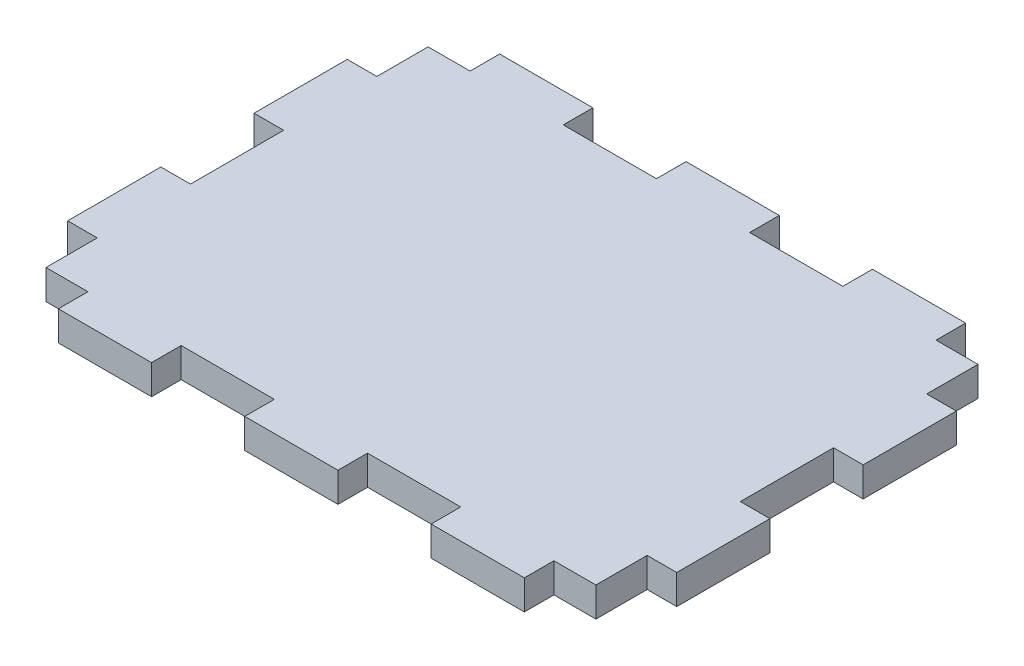
SolidWorks part; units mm, degrees
ref_plane "Front Plane" through (0, 0, 0) normal (0, 0, 1) x (1, 0, 0)
ref_plane "Top Plane" through (0, 0, 0) normal (0, 1, 0) x (1, 0, 0)
ref_plane "Right Plane" through (0, 0, 0) normal (1, 0, 0) x (0, 0, -1)
sketch "Sketch1" plane through (0, 0, 0) normal (0, 1, 0) x (1, 0, 0)
  line L1 (0, 0) -> (65.35, 0)
  line L2 (0, 0) -> (0, 47.35)
  line L3 (0, 47.35) -> (65.35, 47.35)
  line L4 (65.35, 0) -> (65.35, 47.35)
  dimension "D1" = 65.35
  dimension "D2" = 47.35
extrude "Boss-Extrude1" add sketch "Sketch1" along normal blind 3.175
sketch "Sketch2" plane through (0, 0, 0) normal (0, -1, 0) x (1, 0, 0)
  line L0 (65.35, 0) -> (65.35, -47.35) construction
  line L1 (62.175, -38.675) -> (65.35, -38.675)
  line L2 (62.175, -38.675) -> (62.175, -47.35)
  line L3 (62.175, -47.35) -> (65.35, -47.35)
  line L4 (65.35, -38.675) -> (65.35, -47.35)
  line L5 (0, 0) -> (65.35, 0) construction
  line L6 (62.175, -28.675) -> (65.35, -28.675)
  line L7 (62.175, -28.675) -> (62.175, -18.675)
  line L8 (62.175, -18.675) -> (65.35, -18.675)
  line L9 (65.35, -28.675) -> (65.35, -18.675)
  line L10 (62.175, -8.675) -> (65.35, -8.675)
  line L11 (62.175, -8.675) -> (62.175, 0)
  line L12 (62.175, 0) -> (65.35, 0)
  line L13 (65.35, -8.675) -> (65.35, 0)
  line L14 (65.35, -47.35) -> (0, -47.35) construction
  line L15 (0, -47.35) -> (0, 0) construction
  line L16 (0, -47.35) -> (3.175, -47.35)
  line L17 (0, -47.35) -> (0, -38.675)
  line L18 (0, -38.675) -> (3.175, -38.675)
  line L19 (3.175, -47.35) -> (3.175, -38.675)
  line L21 (0, -28.675) -> (3.175, -28.675)
  line L22 (0, -28.675) -> (0, -18.675)
  line L23 (0, -18.675) -> (3.175, -18.675)
  line L24 (3.175, -28.675) -> (3.175, -18.675)
  line L25 (0, 0) -> (3.175, 0)
  line L26 (0, 0) -> (0, -8.675)
  line L27 (0, -8.675) -> (3.175, -8.675)
  line L28 (3.175, 0) -> (3.175, -8.675)
  line L29 (62.175, -47.35) -> (57.675, -47.35)
  line L30 (62.175, -47.35) -> (62.175, -44.175)
  line L31 (62.175, -44.175) -> (57.675, -44.175)
  line L32 (57.675, -47.35) -> (57.675, -44.175)
  line L33 (47.675, -47.35) -> (37.675, -47.35)
  line L34 (47.675, -47.35) -> (47.675, -44.175)
  line L35 (47.675, -44.175) -> (37.675, -44.175)
  line L36 (37.675, -47.35) -> (37.675, -44.175)
  line L37 (27.675, -47.35) -> (17.675, -47.35)
  line L38 (27.675, -47.35) -> (27.675, -44.175)
  line L39 (27.675, -44.175) -> (17.675, -44.175)
  line L40 (17.675, -47.35) -> (17.675, -44.175)
  line L41 (3.175, -47.35) -> (7.675, -47.35)
  line L42 (3.175, -47.35) -> (3.175, -44.175)
  line L43 (3.175, -44.175) -> (7.675, -44.175)
  line L44 (7.675, -47.35) -> (7.675, -44.175)
  line L45 (57.675, -3.175) -> (62.175, -3.175)
  line L46 (57.675, -3.175) -> (57.675, 0)
  line L47 (57.675, 0) -> (62.175, 0)
  line L48 (62.175, -3.175) -> (62.175, 0)
  line L49 (47.675, -3.175) -> (37.675, -3.175)
  line L50 (47.675, -3.175) -> (47.675, 0)
  line L51 (47.675, 0) -> (37.675, 0)
  line L52 (37.675, -3.175) -> (37.675, 0)
  line L53 (27.675, -3.175) -> (17.675, -3.175)
  line L54 (27.675, -3.175) -> (27.675, 0)
  line L55 (27.675, 0) -> (17.675, 0)
  line L56 (17.675, -3.175) -> (17.675, 0)
  line L57 (7.675, -3.175) -> (3.175, -3.175)
  line L58 (7.675, -3.175) -> (7.675, 0)
  line L59 (7.675, 0) -> (3.175, 0)
  line L60 (3.175, -3.175) -> (3.175, 0)
  point P16 (65.35, -23.675)
  point P17 (62.175, -23.675)
  line M30 (0, 0) -> (0, -47.35)
  line M31 (0, -47.35) -> (65.35, -47.35)
  line M32 (65.35, -47.35) -> (65.35, 0)
  line M33 (65.35, 0) -> (0, 0)
  dimension "D1" = 10
  dimension "D2" = 10
  dimension "D3" = 10
  dimension "D4" = 3.175
  dimension "D5" = 3.175
  dimension "D6" = 10
  dimension "D7" = 10
  dimension "D8" = 10
  dimension "D9" = 10
  dimension "D10" = 10
  dimension "D11" = 3.175
  dimension "D12" = 3.175
extrude "Cut-Extrude1" cut sketch "Sketch2" against normal through all contours L32 L2 L31 M31 | L1 L2 M31 M32 | L8 L7 L6 M32 | L11 L10 M32 M33 | L46 L45 L11 M33 | L52 L49 L50 M33 | L36 L34 L35 M31 | L40 L38 L39 M31 | L44 L43 L19 M31 | L19 L18 M31 M30 | L21 L24 L23 M30 | L28 L27 M33 M30 | L57 L58 L28 M33 | L56 L53 L54 M33
